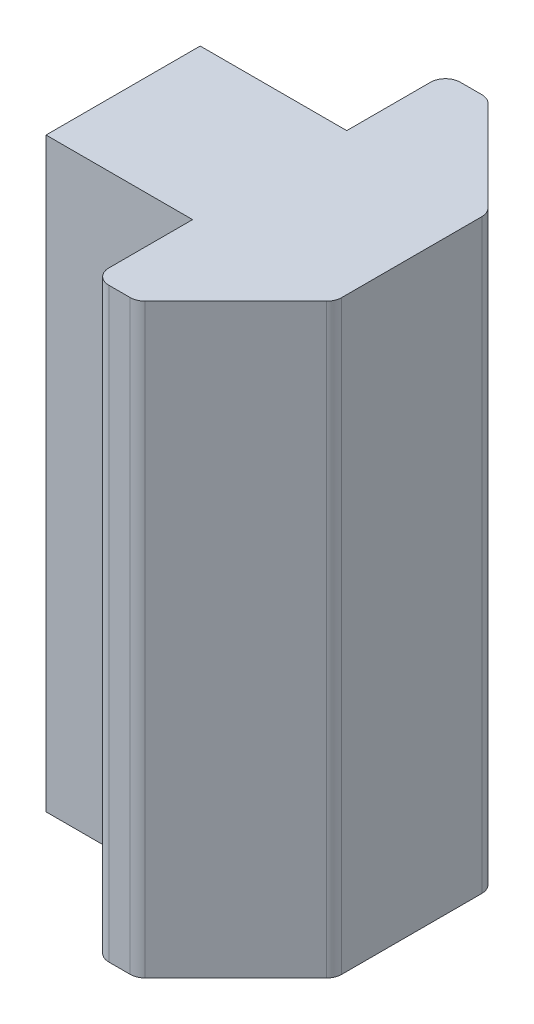
SolidWorks part; units mm, degrees
ref_plane "Front Plane" through (0, 0, 0) normal (0, 0, 1) x (1, 0, 0)
ref_plane "Top Plane" through (0, 0, 0) normal (0, 1, 0) x (1, 0, 0)
ref_plane "Right Plane" through (0, 0, 0) normal (1, 0, 0) x (0, 0, -1)
sketch "Sketch1" plane through (0, 0, 0) normal (0, 1, 0) x (1, 0, 0)
  line L0 (-4.8471, 5.4871) -> (-4.8471, 2.63)
  line L1 (-3.2465, -5.8478) -> (-0.1494, -2.7506)
  line L2 (-4.3371, 5.9971) -> (-3.6071, 5.9971)
  line L3 (-3.2465, 5.8478) -> (-0.1494, 2.7506)
  line L4 (0, 2.39) -> (0, -2.39)
  line L5 (-17.4584, 0) -> (3.8151, 0) construction
  line L6 (-4.3371, -5.9971) -> (-3.6071, -5.9971)
  line L7 (-4.8471, -2.63) -> (-4.8471, -5.4871)
  line L8 (-9.8471, -2.63) -> (-4.8471, -2.63)
  line L9 (-9.8471, -2.63) -> (-9.8471, 2.63)
  line L10 (-9.8471, 2.63) -> (-4.8471, 2.63)
  arc A0 (-0.1494, -2.7506) -> (0, -2.39) centre (-0.51, -2.39) ccw
  arc A1 (-4.8471, 5.4871) -> (-4.3371, 5.9971) centre (-4.3371, 5.4871) cw
  arc A2 (-3.6071, 5.9971) -> (-3.2465, 5.8478) centre (-3.6071, 5.4871) cw
  arc A3 (-0.1494, 2.7506) -> (0, 2.39) centre (-0.51, 2.39) cw
  arc A4 (-3.6071, -5.9971) -> (-3.2465, -5.8478) centre (-3.6071, -5.4871) ccw
  arc A5 (-4.8471, -5.4871) -> (-4.3371, -5.9971) centre (-4.3371, -5.4871) ccw
  point P5 (0, 0)
  point P26 (0, 0)
  point P27 (-9.8471, 0)
  dimension "D3" = 5
  dimension "D6" = 2.39
  dimension "D1" = 0.51
  dimension "D2" = 5.26
  dimension "D4" = 0.73
  dimension "D5" = 4.38
  dimension "D7" = 135
extrude "Boss-Extrude1" add sketch "Sketch1" along normal blind 20
sketch "Sketch2" plane through (-9.8471, 0, 0) normal (-1, 0, 0) x (0, 0, 1)
  line L0 (0, 20) -> (0, 0) construction
  line L1 (-2.63, 20) -> (2.63, 20) construction
  line L2 (-2.63, 0) -> (2.63, 0) construction
  circle A0 centre (0, 10) radius 2.1
  dimension "D1" = 4.2
extrude "Cut-Extrude1" cut sketch "Sketch2" against normal blind 6
